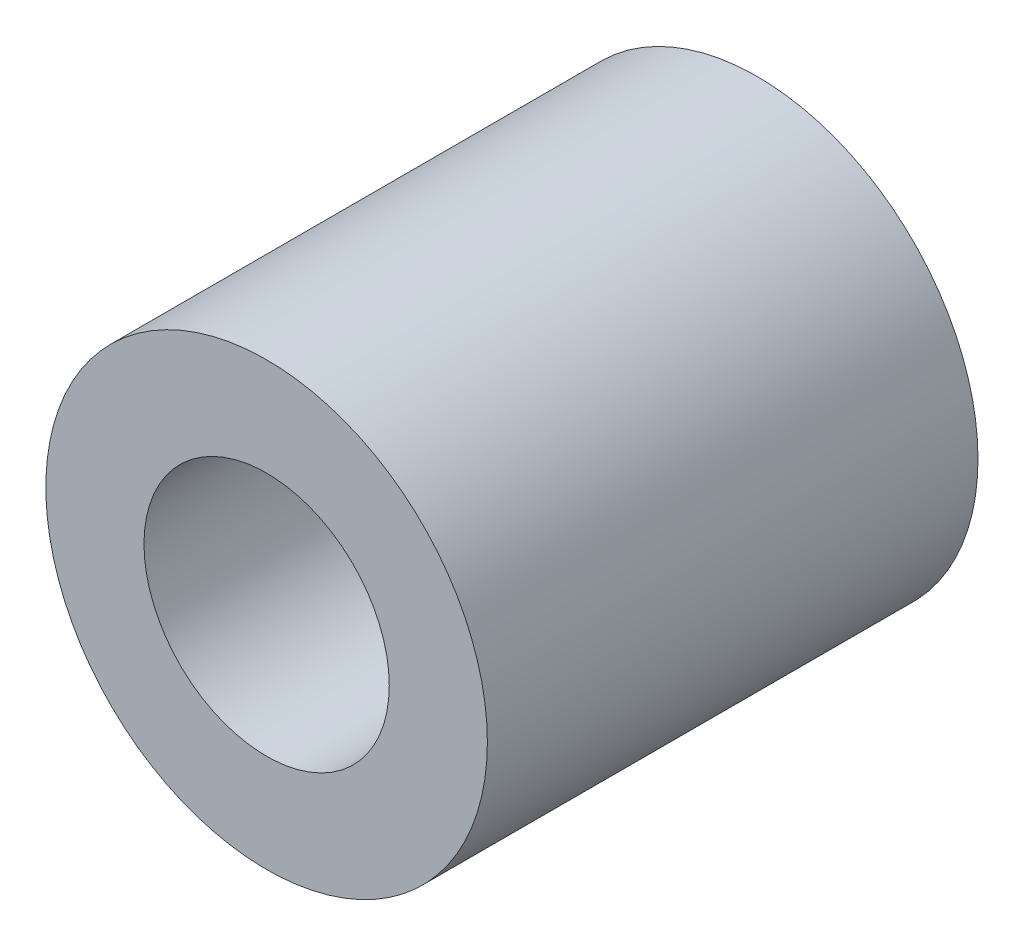
SolidWorks part; units mm, degrees
material "PBT Uniwersalny"
ref_plane "Płaszczyzna przednia" through (0, 0, 0) normal (0, 0, 1) x (1, 0, 0)
ref_plane "Płaszczyzna górna" through (0, 0, 0) normal (0, 1, 0) x (1, 0, 0)
ref_plane "Płaszczyzna prawa" through (0, 0, 0) normal (1, 0, 0) x (0, 0, -1)
sketch "Szkic1" plane through (0, 0, 0) normal (0, 0, 1) x (1, 0, 0)
  circle A1 centre (0, 0) radius 1.75
  circle A2 centre (0, 0) radius 3.15
  dimension "D2" = 3.5
  dimension "D1" = 6.3
extrude "Dodanie-wyciągnięcie1" add sketch "Szkic1" along normal blind 7
